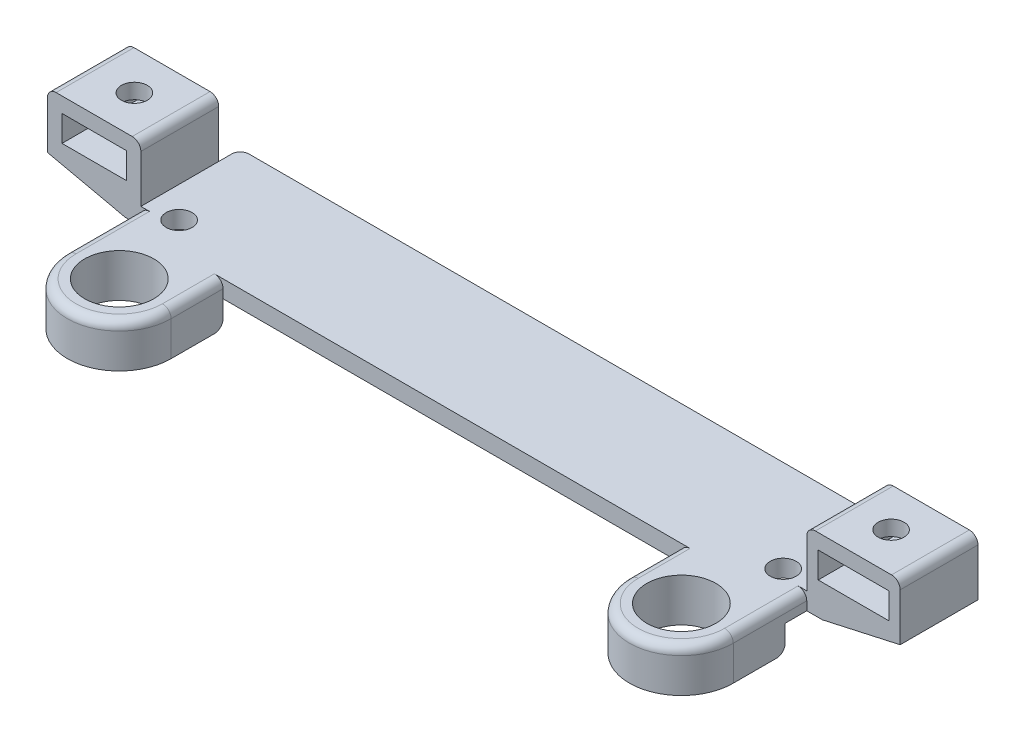
SolidWorks part; units mm, degrees
ref_plane "Front Plane" through (0, 0, 0) normal (0, 0, 1) x (1, 0, 0)
ref_plane "Top Plane" through (0, 0, 0) normal (0, 1, 0) x (1, 0, 0)
ref_plane "Right Plane" through (0, 0, 0) normal (1, 0, 0) x (0, 0, -1)
sketch "Sketch1" plane through (0, 0, 0) normal (0, 1, 0) x (1, 0, 0)
  line L5 (-91.7538, 1.2704) -> (-14.7538, 1.2704)
  line L6 (-91.7538, 1.2704) -> (-91.7538, -12.7296)
  line L7 (-91.7538, -12.7296) -> (-14.7538, -12.7296)
  line L8 (-14.7538, 1.2704) -> (-14.7538, -12.7296)
extrude "Boss-Extrude1" add sketch "Sketch1" along normal blind 2 contours L6 L5 L8 L7
sketch "Sketch3" plane through (-91.7538, 0, 0) normal (-1, 0, 0) x (0, 0, 1)
  line L0 (5.7296, 2) -> (1.2296, 2) construction
  line L1 (-1.2704, 2) -> (12.7296, 2) construction
  line L2 (5.7296, 2) -> (10.2296, 2) construction
  line L3 (10.2296, 2) -> (10.2296, 0) construction
  line L4 (-1.2704, 0) -> (12.7296, 0) construction
  line L6 (1.2296, 2) -> (10.2296, 2)
  line L7 (1.2296, 2) -> (1.2296, 0)
  line L8 (1.2296, 0) -> (10.2296, 0)
  line L9 (10.2296, 2) -> (10.2296, 0)
extrude "Boss-Extrude2" add sketch "Sketch3" along normal blind 10.8 contours L7 L6 L9 L8
sketch "Sketch4" plane through (-14.7538, 0, 0) normal (1, 0, 0) x (0, 0, -1)
  line L0 (-5.7296, 2) -> (-10.2296, 2) construction
  line L1 (1.2704, 2) -> (-12.7296, 2) construction
  line L2 (-10.2296, 2) -> (-10.2296, 0) construction
  line L3 (-5.7296, 2) -> (-1.2296, 2) construction
  line L5 (-10.2296, 2) -> (-1.2296, 2)
  line L6 (-10.2296, 2) -> (-10.2296, 0)
  line L7 (-10.2296, 0) -> (-1.2296, 0)
  line L8 (-1.2296, 2) -> (-1.2296, 0)
extrude "Boss-Extrude3" add sketch "Sketch4" along normal blind 10.8 contours L6 L5 L8 L7
sketch "Sketch5" plane through (0, 2, 0) normal (0, 1, 0) x (1, 0, 0)
  line L9 (-91.7538, -1.2296) -> (-102.5538, -1.2296)
  line L10 (-91.7538, -1.2296) -> (-91.7538, -10.2296)
  line L11 (-91.7538, -10.2296) -> (-102.5538, -10.2296)
  line L12 (-102.5538, -1.2296) -> (-102.5538, -10.2296)
  line L13 (-14.7538, -10.2296) -> (-3.9538, -10.2296)
  line L14 (-14.7538, -10.2296) -> (-14.7538, -1.2296)
  line L15 (-14.7538, -1.2296) -> (-3.9538, -1.2296)
  line L16 (-3.9538, -10.2296) -> (-3.9538, -1.2296)
extrude "Boss-Extrude4" add sketch "Sketch5" along normal blind 6.5
sketch "Sketch6" plane through (0, 0, 10.2296) normal (0, 0, 1) x (1, 0, 0)
  line L0 (-14.7538, 2) -> (-3.9538, 8.5) construction
  line L5 (-102.5538, 8.5) -> (-91.7538, 2) construction
  line L6 (-13.4338, 6.75) -> (-5.2738, 3.75) construction
  line L7 (-13.4338, 6.75) -> (-5.2738, 6.75)
  line L12 (-13.4338, 6.75) -> (-13.4338, 3.75)
  line L13 (-13.4338, 3.75) -> (-5.2738, 3.75)
  line L14 (-5.2738, 6.75) -> (-5.2738, 3.75)
  line L15 (-100.8738, 6.75) -> (-93.4338, 3.75) construction
  line L16 (-100.8738, 6.75) -> (-93.4338, 6.75)
  line L17 (-100.8738, 6.75) -> (-100.8738, 3.75)
  line L18 (-100.8738, 3.75) -> (-93.4338, 3.75)
  line L19 (-93.4338, 6.75) -> (-93.4338, 3.75)
  point P16 (-9.3538, 5.25)
  point P17 (-97.1538, 5.25)
  point P18 (-9.3538, 5.25)
  point P19 (-97.1538, 5.25)
extrude "Cut-Extrude1" cut sketch "Sketch6" against normal up to surface (9 mm away) up to face at (-10.4338, 3.8, 1.2296)
sketch "Sketch8" plane through (0, 8.5, 0) normal (0, 1, 0) x (1, 0, 0)
  line L0 (-53.2538, 0.6204) -> (-90.7188, 0.6204) construction
  line L1 (-53.2538, 0.6204) -> (-15.7888, 0.6204) construction
  line L2 (-90.7188, 0.6204) -> (-90.7188, -12.0796) construction
  line L3 (-90.7188, -12.0796) -> (-15.7888, -12.0796) construction
  line L4 (-15.7888, -12.0796) -> (-15.7888, 0.6204) construction
  line L5 (-18.3288, -9.3796) -> (-88.1788, -9.3796) construction
  line L6 (-53.2538, 0.6204) -> (-53.2538, -9.3796) construction
  line L7 (-53.2538, -9.3796) -> (-53.2538, -12.0796) construction
  line L8 (-91.7538, 1.2704) -> (-14.7538, 1.2704) construction
  line L9 (-91.7538, 1.2704) -> (-14.7538, 1.2704) construction
  line L10 (-14.7538, 1.2704) -> (-14.7538, -1.2296) construction
  circle A0 centre (-88.1788, -9.3796) radius 1.5
  circle A1 centre (-18.3288, -9.3796) radius 1.5
  circle A2 centre (-97.0038, -5.7296) radius 1.5
  circle A3 centre (-9.5038, -5.7296) radius 1.5
extrude "Cut-Extrude2" cut sketch "Sketch8" against normal up to surface (8.5 mm away) up to face at (-53.2538, 0, 5.7296)
sketch "Sketch10" plane through (0, 0, 0) normal (0, -1, 0) x (-1, 0, 0)
  line L0 (102.5538, -10.2296) -> (102.5538, -8.7296) construction
  line L1 (102.5538, -1.2296) -> (102.5538, -10.2296) construction
  line L2 (102.5538, -1.2296) -> (102.5538, -2.7296) construction
  line L3 (91.7538, -10.2296) -> (91.7538, -8.7296) construction
  line L4 (14.7538, -10.2296) -> (14.7538, -8.7296) construction
  line L5 (102.5538, -8.7296) -> (93.2538, -8.7296)
  line L6 (102.5538, -8.7296) -> (102.5538, -2.7296)
  line L7 (102.5538, -2.7296) -> (93.2538, -2.7296)
  line L9 (3.9538, -10.2296) -> (3.9538, -8.7296) construction
  line L10 (3.9538, -10.2296) -> (3.9538, -1.2296) construction
  line L11 (3.9538, -1.2296) -> (3.9538, -2.7296) construction
  line L12 (93.2538, -2.7296) -> (93.2538, -8.7296)
  line L13 (3.9538, -8.7296) -> (13.2538, -8.7296)
  line L14 (3.9538, -8.7296) -> (3.9538, -2.7296)
  line L15 (3.9538, -2.7296) -> (13.2538, -2.7296)
  line L17 (13.2538, -2.7296) -> (13.2538, -8.7296)
  line L18 (14.7538, -2.7296) -> (14.7538, -1.2296) construction
  line L19 (91.7538, -2.7296) -> (91.7538, -1.2296) construction
  point P34 (93.2538, -5.7296)
  point P40 (13.2538, -5.7296)
extrude "Cut-Extrude4" cut sketch "Sketch10" against normal blind 2
chamfer "Chamfer1" distance 9 distance2 2 4 edges at (-102.5538, 0, 1.9796) (-3.9538, 0, 9.4796) (-3.9538, 0, 1.9796) (-102.5538, 0, 9.4796)
sketch "Sketch12" plane through (0, 2, 0) normal (0, 1, 0) x (1, 0, 0)
  line L1 (-91.7538, -12.7296) -> (-14.7538, -12.7296) construction
  line L3 (-26.7538, -12.7296) -> (-14.7538, -12.7296)
  line L4 (-91.7538, -12.7296) -> (-91.7538, -18.7296)
  line L5 (-91.7538, -12.7296) -> (-79.7538, -12.7296)
  line L6 (-79.7538, -18.7296) -> (-79.7538, -12.7296)
  line L7 (-26.7538, -18.7296) -> (-26.7538, -12.7296)
  line L8 (-14.7538, -18.7296) -> (-14.7538, -12.7296)
  arc A0 (-91.7538, -18.7296) -> (-79.7538, -18.7296) centre (-85.7538, -18.7296) ccw
  arc A1 (-26.7538, -18.7296) -> (-14.7538, -18.7296) centre (-20.7538, -18.7296) ccw
extrude "Boss-Extrude5" add sketch "Sketch12" against normal blind 5
sketch "Sketch13" plane through (0, 2, 0) normal (0, 1, 0) x (1, 0, 0)
  circle A0 centre (-85.7538, -18.7296) radius 4
  circle A1 centre (-20.7538, -18.7296) radius 4
extrude "Cut-Extrude5" cut sketch "Sketch13" against normal up to surface (5 mm away) up to face at (-85.7538, -3, 17.2296)
fillet "Fillet3" radius 1 14 edges at (-102.5538, 8.5, 5.7296) (-91.7538, 8.5, 5.7296) (-91.7538, 1, -1.2704) (-14.7538, 1, -1.2704) (-26.7538, 2, 15.7296) (-14.7538, 2, 14.4796) (-91.7538, 2, 14.4796) (-79.7538, 2, 15.7296) (-20.7538, 2, 24.7296) (-85.7538, 2, 24.7296) (-85.7538, -3, 12.7296) (-20.7538, -3, 12.7296) (-14.7538, 8.5, 5.7296) (-3.9538, 8.5, 5.7296)
